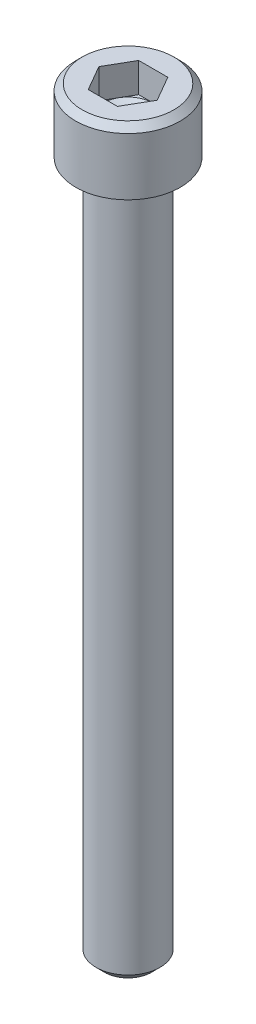
SolidWorks part; units mm, degrees
material "Alloy Steel"
ref_plane "Front Plane" through (0, 0, 0) normal (0, 0, 1) x (1, 0, 0)
ref_plane "Top Plane" through (0, 0, 0) normal (0, 1, 0) x (1, 0, 0)
ref_plane "Right Plane" through (0, 0, 0) normal (1, 0, 0) x (0, 0, -1)
sketch "Sketch1" plane through (0, 0, 0) normal (0, 0, 1) x (1, 0, 0)
  line L0 (2.8702, 3.5052) -> (0, 3.5052)
  line L1 (0, 3.5052) -> (0, 0)
  line L2 (0, 0) -> (2.8702, 0)
  line L3 (2.8702, 0) -> (2.8702, 3.5052)
  line L4 (0, 3.5052) -> (0, 0) construction
revolve "Revolve1" add sketch "Sketch1" angle 360 about L4
sketch "Sketch2" plane through (0, 0, 0) normal (0, -1, 0) x (1, 0, 0)
  circle A0 centre (0, 0) radius 1.7526
extrude "Boss-Extrude1" add sketch "Sketch2" along normal blind 38.1
sketch "Sketch3" plane through (0, 3.5052, 0) normal (0, 1, 0) x (-1, 0, 0)
  line L0 (-0.7992, 1.3843) -> (-1.5985, 0)
  line L1 (-1.5985, 0) -> (-0.7992, -1.3843)
  line L2 (-0.7992, -1.3843) -> (0.7992, -1.3843)
  line L3 (0.7992, -1.3843) -> (1.5985, 0)
  line L4 (1.5985, 0) -> (0.7992, 1.3843)
  line L5 (0.7992, 1.3843) -> (-0.7992, 1.3843)
extrude "Cut-Extrude1" cut sketch "Sketch3" against normal blind 1.6256
sketch "Sketch4" plane through (0, 0, 0) normal (0, 0, 1) x (1, 0, 0)
  line L0 (1.3843, 1.8796) -> (0, 1.8796)
  line L1 (0, 1.8796) -> (0, 1.0804)
  line L2 (0, 1.0804) -> (1.3843, 1.8796)
  line L3 (0, 1.8796) -> (0, 1.0803) construction
revolve "Cut-Revolve1" cut sketch "Sketch4" angle 360 about L3
chamfer "Chamfer1" distance 0.4724 angle 45 1 edges at (0, -38.1, -1.7526)
chamfer "Chamfer2" distance 0.3556 angle 45 1 edges at (0, 3.5052, -2.8702)
fillet "Fillet1" radius 0.254 1 edges at (0, 0, -1.7526)
